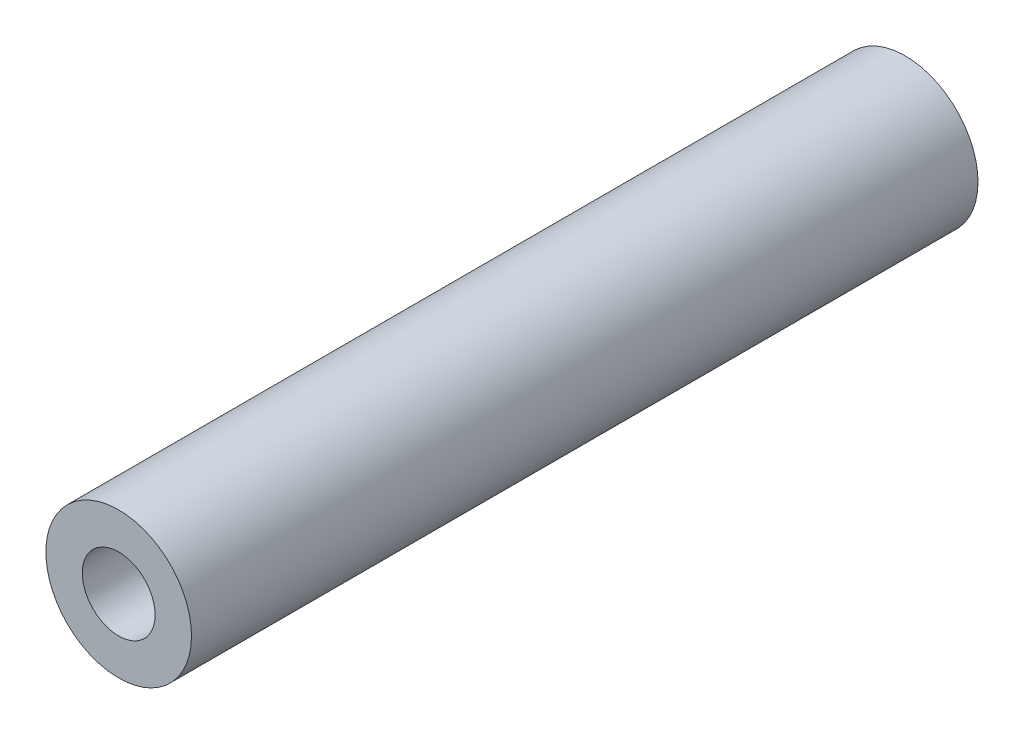
SolidWorks part; units mm, degrees
material "Cobre"
ref_plane "Alzado" through (0, 0, 0) normal (0, 0, 1) x (1, 0, 0)
ref_plane "Planta" through (0, 0, 0) normal (0, 1, 0) x (1, 0, 0)
ref_plane "Vista lateral" through (0, 0, 0) normal (1, 0, 0) x (0, 0, -1)
sketch "Croquis1" plane through (0, 0, 0) normal (0, 0, 1) x (1, 0, 0)
  circle A0 centre (0, 0) radius 1
  circle A1 centre (0, 0) radius 0.5
  dimension "D1" = 2
  dimension "D2" = 1
extrude "Saliente-Extruir1" add sketch "Croquis1" along normal blind 10.8
